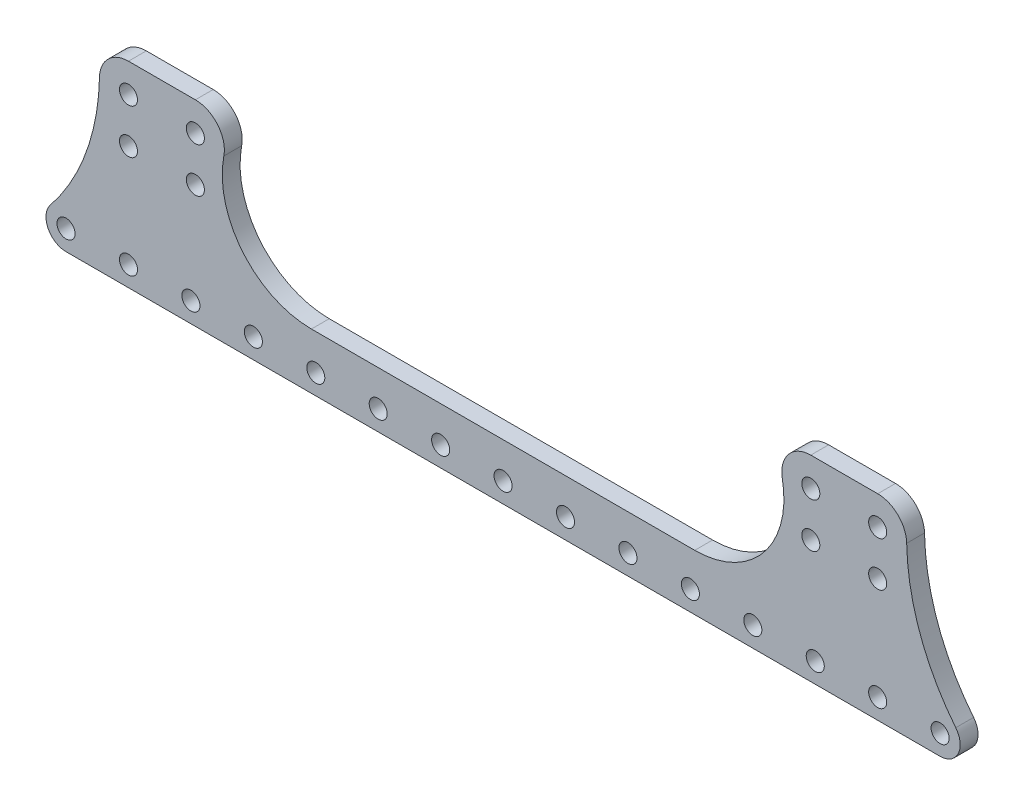
SolidWorks part; units mm, degrees
material "Thornel Mat VMA"
ref_plane "前视基准面" through (0, 0, 0) normal (0, 0, 1) x (1, 0, 0)
ref_plane "上视基准面" through (0, 0, 0) normal (0, 1, 0) x (1, 0, 0)
ref_plane "右视基准面" through (0, 0, 0) normal (1, 0, 0) x (0, 0, -1)
other "Configuration Table"
sketch "草图1" plane through (0, 0, 0) normal (0, 0, 1) x (1, 0, 0)
  line L0 (0, 0) -> (17960.6475, 0) construction
  line L1 (-84, -5) -> (-84, -28) construction
  line L2 (-69, -5) -> (-84, -5) construction
  line L3 (-69, -5) -> (-69, 5) construction
  line L4 (-69, 5) -> (-84, 5) construction
  line L5 (-84, -5) -> (-84, 5) construction
  line L6 (-69, -5) -> (-84, 5) construction
  line L7 (-69, 5) -> (-84, -5) construction
  line L8 (0, 0) -> (0, -50000) construction
  line L9 (69, 5) -> (84, -5) construction
  line L10 (-88, -9) -> (-65, -9) construction
  line L11 (-88, -9) -> (-88, 9) construction
  line L12 (-88, 9) -> (-65, 9) construction
  line L13 (-65, -9) -> (-65, 9) construction
  line L14 (-88, -9) -> (-65, 9) construction
  line L15 (-88, 9) -> (-65, -9) construction
  line L16 (-84, -28) -> (-98, -28) construction
  line L17 (88, -9) -> (65, -9) construction
  line L18 (88, -9) -> (88, 9) construction
  line L19 (88, 9) -> (65, 9) construction
  line L20 (65, -9) -> (65, 9) construction
  line L21 (88, -9) -> (65, 9) construction
  line L22 (88, 9) -> (65, -9) construction
  line L23 (-98, -32.5) -> (98, -32.5)
  line L24 (-42.976, -20) -> (42.976, -20)
  line L25 (84, -28) -> (98, -28) construction
  line L26 (88, 9) -> (65, -9) construction
  line L27 (88, -9) -> (65, 9) construction
  line L28 (65, -9) -> (65, 9) construction
  line L29 (88, 9) -> (65, 9) construction
  line L30 (88, -9) -> (88, 9) construction
  line L31 (88, -9) -> (65, -9) construction
  line L32 (69, 5) -> (84, -5) construction
  line L33 (69, -5) -> (84, 5) construction
  line L34 (84, -5) -> (84, 5) construction
  line L35 (69, 5) -> (84, 5) construction
  line L36 (69, -5) -> (69, 5) construction
  line L37 (69, -5) -> (84, -5) construction
  line L38 (84, -5) -> (84, -28) construction
  line L39 (0, 0) -> (-17960.6475, 0) construction
  line L40 (-84, 11.5) -> (-69, 11.5)
  line L41 (69, 11.5) -> (84, 11.5)
  circle A0 centre (-84, 5) radius 2.025
  circle A1 centre (-69, 5) radius 2.025
  circle A2 centre (-84, -5) radius 2.025
  circle A3 centre (-69, -5) radius 2.025
  circle A4 centre (-84, -28) radius 2.025
  circle A5 centre (84, -5) radius 2.025
  circle A6 centre (69, -5) radius 2.025
  circle A7 centre (69, 5) radius 2.025
  circle A8 centre (84, 5) radius 2.025
  circle A9 centre (-140.4887, 6.1316) radius 50
  circle A10 centre (-84, 5) radius 6.5
  circle A11 centre (-84, -28) radius 6.5 construction
  circle A12 centre (-84, -28) radius 4.5
  circle A13 centre (-98, -28) radius 2.025
  circle A14 centre (-98, -28) radius 4.5
  circle A15 centre (-69, 5) radius 6.5
  circle A17 centre (-42.976, 0) radius 20
  circle A18 centre (-70, -28) radius 2.025
  circle A19 centre (-56, -28) radius 2.025
  circle A20 centre (-42, -28) radius 2.025
  circle A21 centre (-28, -28) radius 2.025
  circle A22 centre (-14, -28) radius 2.025
  circle A23 centre (0, -28) radius 2.025
  circle A24 centre (84, -28) radius 6.5 construction
  circle A25 centre (14, -28) radius 2.025
  circle A26 centre (28, -28) radius 2.025
  circle A27 centre (42, -28) radius 2.025
  circle A28 centre (56, -28) radius 2.025
  circle A29 centre (70, -28) radius 2.025
  circle A30 centre (42.976, 0) radius 20
  circle A31 centre (69, 5) radius 6.5
  circle A32 centre (98, -28) radius 4.5
  circle A33 centre (98, -28) radius 2.025
  circle A34 centre (84, -28) radius 4.5
  circle A35 centre (84, 5) radius 6.5
  circle A36 centre (140.4887, 6.1316) radius 50
  circle A37 centre (84, -28) radius 2.025
  circle A38 centre (69, -5) radius 2.025
  circle A39 centre (84, -5) radius 2.025
  circle A40 centre (69, 5) radius 2.025
  circle A41 centre (84, 5) radius 2.025
  point P3 (-76.5, 0)
  point P24 (-76.5, 0)
  point P29 (76.5, 0)
  point P91 (0, -20)
  point P92 (0, -32.5)
  dimension "D3" = 4.05
  dimension "D5" = 4.05
  dimension "D8" = 4
  dimension "D9" = 13
  dimension "D10" = 100
  dimension "D11" = 13
  dimension "D12" = 9
  dimension "D14" = 40
  dimension "D1" = 10
  dimension "D2" = 15
  dimension "D4" = 84
  dimension "D6" = 23
  dimension "D7" = 4
  dimension "D13" = 14
  dimension "D15" = 7
extrude "凸台-拉伸1" add sketch "草图1" along normal blind 4 contours A10 A0 | A15 A1 | A32 A36 A35 L41 A31 A30 L24 A17 A15 L40 A10 A9 A14 L23 A12 A34 A28 A26 A6 A2 A3 A5 A18 A19 A20 A21 A22 A23 A25 A27 A29 | A14 A13 | A12 A4 | A32 A33 | A34 A37 | A31 A7 | A35 A8
sketch "草图2" plane through (0, 0, 4) normal (0, 0, 1) x (1, 0, 0)
  circle A0 centre (-98, -28) radius 6.5 construction
  dimension "D1" = 13
